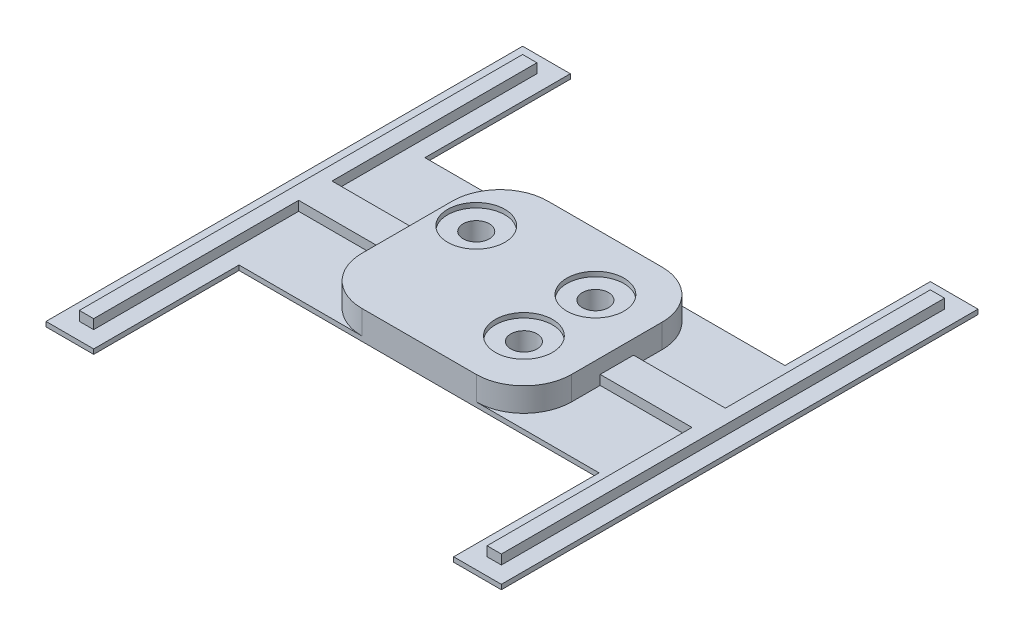
SolidWorks part; units mm, degrees
ref_plane "Front Plane" through (0, 0, 0) normal (0, 0, 1) x (1, 0, 0)
ref_plane "Top Plane" through (0, 0, 0) normal (0, 1, 0) x (1, 0, 0)
ref_plane "Right Plane" through (0, 0, 0) normal (1, 0, 0) x (0, 0, -1)
sketch "Sketch1" plane through (0, 0, 0) normal (0, 1, 0) x (1, 0, 0)
  line L0 (10.9886, 2.4135) -> (10.9886, -12.5865) construction
  line L1 (10.9886, -12.5865) -> (-14.0114, 2.4135) construction
  line L2 (-14.0114, 2.4135) -> (10.9886, 2.4135) construction
  line L4 (-11.0114, -24.5865) -> (12.9886, -24.5865)
  line L5 (-21.0114, -14.5865) -> (-21.0114, 4.4135)
  line L6 (-11.0114, 14.4135) -> (12.9886, 14.4135)
  line L7 (22.9886, -14.5865) -> (22.9886, 4.4135)
  circle A1 centre (-14.0114, 2.4135) radius 1.75
  circle A2 centre (10.9886, 2.4135) radius 1.75
  circle A3 centre (10.9886, -12.5865) radius 1.75
  arc A4 (12.9886, 14.4135) -> (22.9886, 4.4135) centre (12.9886, 4.4135) cw
  arc A5 (12.9886, -24.5865) -> (22.9886, -14.5865) centre (12.9886, -14.5865) ccw
  arc A6 (-11.0114, -24.5865) -> (-21.0114, -14.5865) centre (-11.0114, -14.5865) cw
  arc A7 (-21.0114, 4.4135) -> (-11.0114, 14.4135) centre (-11.0114, 4.4135) cw
  point P6 (0, 0)
  point P7 (-1.5114, -5.0865)
  dimension "D2" = 3.5
  dimension "D8" = 10
  dimension "D1" = 15
  dimension "D3" = 25
  dimension "D4" = 12
  dimension "D5" = 12
  dimension "D6" = 12
  dimension "D7" = 7
extrude "Boss-Extrude1" add sketch "Sketch1" along normal blind 6
sketch "Sketch2" plane through (0, 6, 0) normal (0, 1, 0) x (1, 0, 0)
  circle A0 centre (-14.0114, 2.4135) radius 2.75
  circle A1 centre (10.9886, 2.4135) radius 2.75
  circle A2 centre (10.9886, -12.5865) radius 2.75
  dimension "D1" = 5.5
extrude "Cut-Extrude1" cut sketch "Sketch2" against normal offset from surface (5 mm away) 1 up to face at (10.9886, 0, -0.6635)
sketch "Sketch3" plane through (0, 6, 0) normal (0, 1, 0) x (1, 0, 0)
  circle A0 centre (10.9886, 2.4135) radius 6
  circle A1 centre (10.9886, -12.5865) radius 6
  circle A2 centre (-14.0114, 2.4135) radius 6
  dimension "D1" = 12
extrude "Cut-Extrude2" cut sketch "Sketch3" against normal blind 1
sketch "Sketch4" plane through (0, 0, 0) normal (0, -1, 0) x (1, 0, 0)
  line L0 (-18.0824, 21.6576) -> (20.0597, -11.4846) construction
  line L1 (0.9886, 5.0865) -> (45.0562, 5.0865) construction
  line L2 (-46.7764, -44.9135) -> (-36.7764, -44.9135)
  line L3 (-46.7764, -44.9135) -> (-46.7764, 55.0865)
  line L4 (-46.7764, 55.0865) -> (-36.7764, 55.0865)
  line L5 (48.7537, -44.9135) -> (48.7537, 55.0865)
  line L6 (-46.7764, -44.9135) -> (48.7537, 55.0865) construction
  line L7 (-46.7764, 55.0865) -> (48.7537, -44.9135) construction
  line L9 (-36.7764, 55.0865) -> (-36.7764, 24.5865)
  line L10 (-36.7764, 24.5865) -> (38.7537, 24.5865)
  line L11 (38.7537, 55.0865) -> (38.7537, 24.5865)
  line L12 (-36.7764, -14.4135) -> (38.7537, -14.4135)
  line L13 (38.7537, -44.9135) -> (38.7537, -14.4135)
  line L15 (-36.7764, -44.9135) -> (-36.7764, -14.4135)
  line L16 (38.7537, -44.9135) -> (48.7537, -44.9135)
  line L17 (38.7537, 55.0865) -> (48.7537, 55.0865)
  line L20 (12.9886, -14.4135) -> (-11.0114, -14.4135) construction
  arc A0 (-11.0114, 24.5865) -> (-21.0114, 14.5865) centre (-11.0114, 14.5865) ccw construction
  arc A1 (12.9886, -14.4135) -> (22.9886, -4.4135) centre (12.9886, -4.4135) ccw construction
  point P8 (0.9886, 5.0865)
  dimension "D1" = 100
  dimension "D2" = 10
extrude "Boss-Extrude3" add sketch "Sketch4" against normal blind 1
sketch "Sketch6" plane through (0, 1, 0) normal (0, 1, 0) x (1, 0, 0)
  line L0 (22.9886, -1.5865) -> (42.2537, -1.5865)
  line L1 (22.9886, -14.5865) -> (22.9886, 4.4135) construction
  line L2 (42.2537, -1.5865) -> (42.2537, 41.4052)
  line L3 (42.2537, 41.4052) -> (45.2537, 41.4052)
  line L4 (45.2537, 41.4052) -> (45.2537, -51.5865)
  line L5 (45.2537, -51.5865) -> (42.2537, -51.5865)
  line L6 (42.2537, -51.5865) -> (42.2537, -8.5865)
  line L7 (42.2537, -8.5865) -> (22.9886, -8.5865)
  line L8 (22.9886, -8.5865) -> (22.9886, -1.5865)
  line L9 (48.7537, 44.9135) -> (48.7537, -55.0865) construction
  line L10 (38.7537, -55.0865) -> (38.7537, -24.5865) construction
  line L11 (48.7537, -55.0865) -> (38.7537, -55.0865) construction
  line L12 (22.9886, -5.0865) -> (58.1614, -5.0865) construction
  line L13 (0.9886, 14.4135) -> (0.9886, 27.9387) construction
  line L14 (12.9886, 14.4135) -> (-11.0114, 14.4135) construction
  line L15 (-21.0114, -8.5865) -> (-21.0114, -1.5865)
  line L16 (-40.2764, -8.5865) -> (-21.0114, -8.5865)
  line L17 (-40.2764, -51.5865) -> (-40.2764, -8.5865)
  line L18 (-43.2764, -51.5865) -> (-40.2764, -51.5865)
  line L19 (-43.2764, 41.4052) -> (-43.2764, -51.5865)
  line L20 (-40.2764, 41.4052) -> (-43.2764, 41.4052)
  line L21 (-40.2764, -1.5865) -> (-40.2764, 41.4052)
  line L22 (-21.0114, -1.5865) -> (-40.2764, -1.5865)
  point P18 (22.9886, -5.0865)
  dimension "D2" = 3.5
  dimension "D1" = 3.5
  dimension "D3" = 3.5
  dimension "D4" = 7
extrude "Boss-Extrude4" add sketch "Sketch6" along normal blind 2
sketch "Sketch7" plane through (0, 0, 0) normal (0, -1, 0) x (1, 0, 0)
  circle A0 centre (-14.0114, -2.4135) radius 2
  circle A1 centre (10.9886, -2.4135) radius 2
  circle A2 centre (10.9886, 12.5865) radius 2
  dimension "D1" = 4
extrude "Cut-Extrude3" cut sketch "Sketch7" against normal blind 2
equation "\"D6@Sketch1\"=\"D4@Sketch1\""
equation "\"D1@Sketch6\"=3.5"
equation "\"D2@Sketch6\"=\"D1@Sketch6\""
equation "\"D3@Sketch6\"=\"D1@Sketch6\""
equation "\"D4@Sketch6\"=\"D1@Sketch6\"*2"
